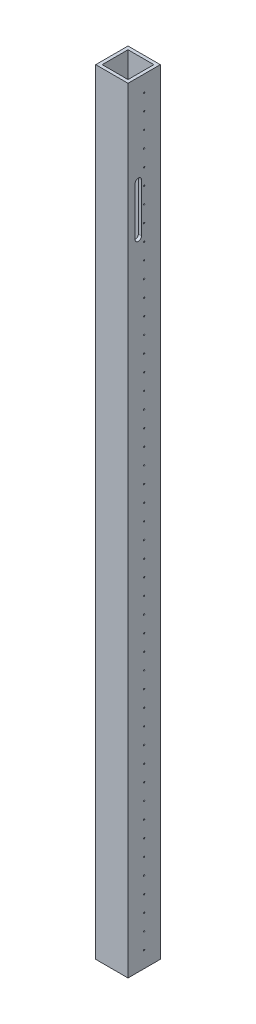
SolidWorks part; units mm, degrees
ref_plane "Front Plane" through (0, 0, 0) normal (0, 0, 1) x (1, 0, 0)
ref_plane "Top Plane" through (0, 0, 0) normal (0, 1, 0) x (1, 0, 0)
ref_plane "Right Plane" through (0, 0, 0) normal (1, 0, 0) x (0, 0, -1)
sketch "Sketch1" plane through (0, 0, 0) normal (0, 1, 0) x (1, 0, 0)
  line L0 (-2.54, -2.54) -> (-2.54, 22.86)
  line L1 (0, 0) -> (20.32, 0)
  line L2 (0, 0) -> (0, 20.32)
  line L3 (0, 20.32) -> (20.32, 20.32)
  line L4 (20.32, 0) -> (20.32, 20.32)
  line L5 (-2.54, 22.86) -> (22.86, 22.86)
  line L6 (22.86, -2.54) -> (22.86, 22.86)
  line L7 (-2.54, -2.54) -> (22.86, -2.54)
  dimension "D1" = 25.4
  dimension "D2" = 25.4
  dimension "D3" = 20.32
extrude "Boss-Extrude1" add sketch "Sketch1" along normal blind 609.6
sketch "Sketch2" plane through (22.86, 0, 0) normal (1, 0, 0) x (0, 0, -1)
  line L0 (10.16, 609.6) -> (10.16, 0) construction
  line L1 (-2.54, 609.6) -> (22.86, 609.6) construction
  line L2 (-2.54, 0) -> (22.86, 0) construction
  circle A1 centre (10.16, 596.9) radius 0.5
  circle A2 centre (10.16, 584.2) radius 0.5
  circle A3 centre (10.16, 571.5) radius 0.5
  circle A4 centre (10.16, 558.8) radius 0.5
  circle A5 centre (10.16, 546.1) radius 0.5
  circle A6 centre (10.16, 533.4) radius 0.5
  circle A7 centre (10.16, 520.7) radius 0.5
  circle A8 centre (10.16, 508) radius 0.5
  circle A9 centre (10.16, 495.3) radius 0.5
  circle A10 centre (10.16, 482.6) radius 0.5
  circle A11 centre (10.16, 469.9) radius 0.5
  circle A12 centre (10.16, 457.2) radius 0.5
  circle A13 centre (10.16, 444.5) radius 0.5
  circle A14 centre (10.16, 431.8) radius 0.5
  circle A15 centre (10.16, 419.1) radius 0.5
  circle A16 centre (10.16, 406.4) radius 0.5
  circle A17 centre (10.16, 393.7) radius 0.5
  circle A18 centre (10.16, 381) radius 0.5
  circle A19 centre (10.16, 368.3) radius 0.5
  circle A20 centre (10.16, 355.6) radius 0.5
  circle A21 centre (10.16, 342.9) radius 0.5
  circle A22 centre (10.16, 330.2) radius 0.5
  circle A23 centre (10.16, 317.5) radius 0.5
  circle A24 centre (10.16, 304.8) radius 0.5
  circle A25 centre (10.16, 292.1) radius 0.5
  circle A26 centre (10.16, 279.4) radius 0.5
  circle A27 centre (10.16, 266.7) radius 0.5
  circle A28 centre (10.16, 254) radius 0.5
  circle A29 centre (10.16, 241.3) radius 0.5
  circle A30 centre (10.16, 228.6) radius 0.5
  circle A31 centre (10.16, 215.9) radius 0.5
  circle A32 centre (10.16, 203.2) radius 0.5
  circle A33 centre (10.16, 190.5) radius 0.5
  circle A34 centre (10.16, 177.8) radius 0.5
  circle A35 centre (10.16, 165.1) radius 0.5
  circle A36 centre (10.16, 152.4) radius 0.5
  circle A37 centre (10.16, 139.7) radius 0.5
  circle A38 centre (10.16, 127) radius 0.5
  circle A39 centre (10.16, 114.3) radius 0.5
  circle A40 centre (10.16, 101.6) radius 0.5
  circle A41 centre (10.16, 88.9) radius 0.5
  circle A42 centre (10.16, 76.2) radius 0.5
  circle A43 centre (10.16, 63.5) radius 0.5
  circle A44 centre (10.16, 50.8) radius 0.5
  circle A45 centre (10.16, 38.1) radius 0.5
  circle A46 centre (10.16, 25.4) radius 0.5
  circle A47 centre (10.16, 12.7) radius 0.5
  dimension "D1" = 1
  dimension "D2" = 12.7
  dimension "D3" = 47
extrude "Cut-Extrude2" cut sketch "Sketch2" against normal blind 62.23
sketch "Sketch4" plane through (22.86, 0, 0) normal (1, 0, 0) x (0, 0, -1)
  line L2 (8.128, 538.48) -> (8.128, 500.38)
  line L3 (3.048, 538.48) -> (3.048, 500.38)
  line L5 (5.588, 538.48) -> (5.588, 500.38)
  line L6 (5.588, 538.48) -> (-2.54, 538.48)
  line L7 (-2.54, 538.48) -> (-2.54, 500.38)
  line L8 (5.588, 500.38) -> (-2.54, 500.38)
  line L10 (5.588, 538.48) -> (5.588, 609.6)
  line L11 (5.588, 538.48) -> (22.86, 538.48)
  line L12 (22.86, 538.48) -> (22.86, 609.6)
  line L13 (5.588, 609.6) -> (22.86, 609.6)
  arc A2 (3.048, 500.38) -> (8.128, 500.38) centre (5.588, 500.38) ccw
  arc A3 (8.128, 538.48) -> (3.048, 538.48) centre (5.588, 538.48) ccw
extrude "Cut-Extrude4" cut sketch "Sketch4" against normal blind 111.76 contours L11 A3 L10 | L10 A3 L6 | L8 L5 L6 L3 | L8 A2 L2 L11 L5
